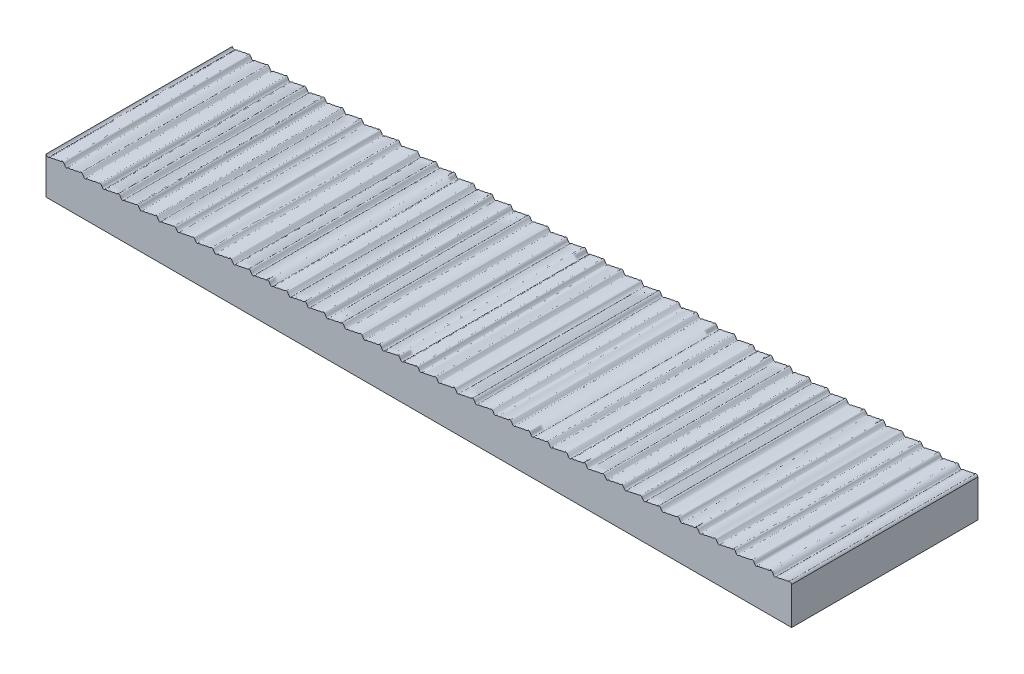
SolidWorks part; units mm, degrees
ref_plane "Ebene vorne" through (0, 0, 0) normal (0, 0, 1) x (1, 0, 0)
ref_plane "Ebene oben" through (0, 0, 0) normal (0, 1, 0) x (1, 0, 0)
ref_plane "Ebene rechts" through (0, 0, 0) normal (1, 0, 0) x (0, 0, -1)
sketch "Skizze1" plane through (0, 0, 0) normal (0, 0, 1) x (1, 0, 0)
  line L0 (0, 10) -> (200, 10) construction
  line L1 (0, 9.5015) -> (200, 9.5015) construction
  line L2 (0, 10) -> (0, 0)
  line L3 (0, 0) -> (200, 0)
  line L4 (200, 10) -> (200, 0)
  line L5 (5.0024, 10) -> (5.0024, 0) construction
  spline S0 degree 4 poles (-19.9997, 10.0004) (-19.9561, 9.9393) (-19.8702, 9.8101) (-19.7695, 9.5768) (-19.4484, 9.4333) (-19.1776, 9.6437) (-18.9243, 9.8025) (-18.5526, 9.7578) (-18.1555, 9.7858) (-17.7539, 10.092) (-17.2072, 9.9072) (-16.8128, 10.2432) (-16.411, 10.2274) (-16.0478, 10.2076) (-15.8056, 10.3731) (-15.5379, 10.5654) (-15.239, 10.4178) (-15.109, 10.1453) (-14.9267, 9.9253) (-14.8002, 9.6012) (-14.3654, 9.35) (-14.0196, 9.9267) (-13.4696, 9.656) (-13.0108, 9.9529) (-12.5208, 10.0184) (-12.0494, 9.999) (-11.6793, 10.2867) (-11.286, 10.195) (-10.9422, 10.2339) (-10.6975, 10.5008) (-10.3481, 10.5321) (-10.1558, 10.2486) (-9.9931, 9.9984) (-9.8662, 9.7615) (-9.5445, 9.3399) (-9.1467, 9.7133) (-8.7378, 9.8283) (-8.2063, 9.709) (-7.8111, 10.0928) (-7.3039, 9.9246) (-6.9101, 10.1513) (-6.5245, 10.2729) (-6.0945, 10.1604) (-5.8142, 10.3786) (-5.4938, 10.5774) (-5.2167, 10.3703) (-5.0931, 10.1352) (-4.9179, 9.9003) (-4.795, 9.6045) (-4.4149, 9.3823) (-4.0837, 9.7842) (-3.6892, 9.7915) (-3.2241, 9.7344) (-2.8526, 10.0555) (-2.3492, 9.9445) (-1.9311, 10.1231) (-1.4459, 10.3184) (-0.9596, 10.0819) (-0.5308, 10.785) (-0.092, 10.1614) (0.0169, 9.9695) (0.2349, 9.6114) (0.4997, 9.4251) (0.8435, 9.6511) (1.1124, 9.8359) (1.5017, 9.7362) (1.8057, 9.8153) (2.0544, 9.9415) (2.3055, 10.0076) (2.5787, 9.9953) (2.8778, 10.016) (3.1891, 10.2002) (3.549, 10.2647) (4.0061, 10.1497) (4.2833, 10.5328) (4.702, 10.5168) (4.8822, 10.1617) (5.0607, 9.9339) (5.1997, 9.6313) (5.5064, 9.4113) (5.8209, 9.6409) (6.0917, 9.8146) (6.4582, 9.7552) (6.7962, 9.7866) (7.1194, 9.9965) (7.4888, 10.0034) (7.8588, 9.9936) (8.1922, 10.2082) (8.5409, 10.2506) (8.9496, 10.1737) (9.2146, 10.416) (9.58, 10.5878) (9.8433, 10.2719) (9.9989, 10.0022) (10.1563, 9.728) (10.4232, 9.4068) (10.7886, 9.59) (11.0551, 9.8225) (11.4498, 9.752) (11.7948, 9.7868) (12.1246, 9.998) (12.4939, 10.0025) (12.8637, 9.9953) (13.1968, 10.2111) (13.5462, 10.2492) (13.9548, 10.1743) (14.2183, 10.4214) (14.5863, 10.5859) (14.8452, 10.2663) (15.0021, 9.9987) (15.1582, 9.7222) (15.4295, 9.4052) (15.7922, 9.5954) (16.0602, 9.823) (16.455, 9.7508) (16.7993, 9.7893) (17.1292, 9.9999) (17.4986, 10.0011) (17.8685, 9.9974) (18.1999, 10.2127) (18.5525, 10.2491) (18.9557, 10.1728) (19.2232, 10.4273) (19.5922, 10.5837) (19.8472, 10.2608) (20.0052, 9.9953) (20.1602, 9.7165) (20.4358, 9.4038) (20.7959, 9.6007) (21.0654, 9.8235) (21.4603, 9.7495) (21.8039, 9.7919) (22.1339, 10.0019) (22.5039, 9.9999) (22.8733, 9.9993) (23.2045, 10.2154) (23.5579, 10.2478) (23.9608, 10.1736) (24.227, 10.4327) (24.5984, 10.5816) (24.8491, 10.2554) (25.0084, 9.9918) (25.1623, 9.7108) (25.4422, 9.4025) (25.7994, 9.606) (26.0707, 9.8238) (26.4655, 9.7483) (26.8086, 9.7945) (27.1386, 10.0038) (27.5093, 9.9987) (27.878, 10.0013) (28.2092, 10.2179) (28.5633, 10.2463) (28.9658, 10.1744) (29.2308, 10.438) (29.6045, 10.5793) (29.851, 10.25) (30.0116, 9.9884) (30.1643, 9.705) (30.4486, 9.4014) (30.8029, 9.6113) (31.076, 9.8242) (31.4707, 9.7472) (31.8132, 9.7971) (32.1433, 10.0056) (32.5147, 9.9975) (32.8827, 10.0034) (33.2139, 10.2205) (33.5687, 10.2449) (33.9708, 10.1753) (34.2347, 10.4433) (34.6105, 10.5768) (34.8528, 10.2446) (35.0148, 9.985) (35.1663, 9.6993) (35.4549, 9.4004) (35.8063, 9.6165) (36.0813, 9.8244) (36.4759, 9.746) (36.8179, 9.7998) (37.148, 10.0075) (37.5201, 9.9962) (37.8873, 10.0057) (38.2187, 10.2227) (38.5737, 10.2439) (38.9763, 10.1755) (39.2407, 10.4527) (39.6307, 10.576) (39.8665, 10.2116) (40.0383, 9.9585) (40.1921, 9.6374) (40.5168, 9.4039) (40.8355, 9.6598) (41.1108, 9.8146) (41.4929, 9.7484) (41.8256, 9.8036) (42.153, 10.0098) (42.5253, 9.9946) (42.8921, 10.008) (43.2233, 10.225) (43.5792, 10.2424) (43.981, 10.1766) (44.2447, 10.458) (44.6365, 10.573) (44.8682, 10.2065) (45.0412, 9.9553) (45.1946, 9.6316) (45.5229, 9.4047) (45.8387, 9.6643) (46.1164, 9.8146) (46.4978, 9.7474) (46.8303, 9.8065) (47.1577, 10.0114) (47.5307, 9.9935) (47.8968, 10.0101) (48.2278, 10.2277) (48.5849, 10.2403) (48.9852, 10.1788) (49.2459, 10.4577) (49.6244, 10.5683) (49.8544, 10.2369) (50.0188, 9.9811) (50.166, 9.6982) (50.4577, 9.4005) (50.8095, 9.6157) (51.0859, 9.829) (51.4904, 9.7412) (51.8293, 9.8082) (52.1631, 10.012) (52.5356, 9.9928) (52.9017, 10.0121) (53.2323, 10.2301) (53.5904, 10.2387) (53.9899, 10.1802) (54.2499, 10.4628) (54.6301, 10.5654) (54.8562, 10.2318) (55.0219, 9.9776) (55.1681, 9.6925) (55.464, 9.3997) (55.8131, 9.6212) (56.0912, 9.8289) (56.4956, 9.7403) (56.8339, 9.811) (57.1679, 10.0136) (57.541, 9.9916) (57.9063, 10.0144) (58.2369, 10.2323) (58.5958, 10.2371) (58.9945, 10.1815) (59.254, 10.4678) (59.6359, 10.5624) (59.858, 10.2269) (60.025, 9.9741) (60.1702, 9.6868) (60.4702, 9.3989) (60.8166, 9.6266) (61.0966, 9.8287) (61.5007, 9.7394) (61.8385, 9.8139) (62.1727, 10.0151) (62.5463, 9.9904) (62.911, 10.0168) (63.2416, 10.2345) (63.6012, 10.2355) (63.9991, 10.183) (64.2582, 10.4728) (64.6415, 10.5592) (64.8598, 10.2219) (65.0281, 9.9707) (65.1724, 9.6811) (65.4765, 9.3984) (65.8201, 9.632) (66.102, 9.8284) (66.5058, 9.7385) (66.8431, 9.8168) (67.1775, 10.0165) (67.5516, 9.9893) (67.9156, 10.0192) (68.2462, 10.2366) (68.6067, 10.2339) (69.0036, 10.1846) (69.2623, 10.4778) (69.647, 10.556) (69.8615, 10.2171) (70.0311, 9.9672) (70.1746, 9.6754) (70.4827, 9.398) (70.8236, 9.6374) (71.1074, 9.8281) (71.5109, 9.7377) (71.8477, 9.8197) (72.1824, 10.0179) (72.5569, 9.9881) (72.9202, 10.0217) (73.2508, 10.2387) (73.6122, 10.2323) (74.008, 10.1863) (74.2666, 10.4827) (74.6525, 10.5526) (74.8633, 10.2123) (75.0342, 9.9637) (75.1768, 9.6697) (75.4889, 9.3977) (75.827, 9.6427) (76.1129, 9.8278) (76.5159, 9.7369) (76.8526, 9.8228) (77.1873, 10.0192) (77.563, 9.9871) (77.9249, 10.0241) (78.2569, 10.2418) (78.618, 10.2295) (79.0102, 10.1872) (79.2717, 10.4879) (79.6574, 10.5489) (79.8653, 10.2077) (80.037, 9.9602) (80.1792, 9.664) (80.495, 9.3976) (80.8303, 9.648) (81.1184, 9.8273) (81.521, 9.7361) (81.8572, 9.8259) (82.1922, 10.0204) (82.5683, 9.986) (82.9296, 10.0267) (83.2615, 10.2437) (83.6237, 10.2278) (84.0145, 10.189) (84.276, 10.4926) (84.6627, 10.5453) (84.8671, 10.2031) (85.0399, 9.9567) (85.1815, 9.6584) (85.5012, 9.3976) (85.8337, 9.6533) (86.124, 9.8268) (86.526, 9.7354) (86.8618, 9.8289) (87.1971, 10.0216) (87.5736, 9.9849) (87.9342, 10.0293) (88.2661, 10.2456) (88.6293, 10.2262) (89.0188, 10.191) (89.2804, 10.4973) (89.668, 10.5416) (89.8688, 10.1985) (90.0429, 9.9532) (90.1839, 9.6527) (90.5073, 9.3978) (90.837, 9.6585) (91.1296, 9.8263) (91.531, 9.7348) (91.8666, 9.832) (92.202, 10.0228) (92.5793, 9.9837) (92.9389, 10.0323) (93.2714, 10.2474) (93.6347, 10.2247) (94.0244, 10.193) (94.2842, 10.501) (94.6728, 10.5389) (94.871, 10.1929) (95.0455, 9.9509) (95.1865, 9.6454) (95.5132, 9.4008) (95.8406, 9.6584) (96.1347, 9.8335) (96.5739, 9.7092) (96.9573, 9.9087) (97.4027, 10.049) (97.928, 9.9505) (98.349, 10.3706) (98.9393, 10.0547) (99.2714, 10.5624) (99.7397, 10.4986) (99.9143, 10.1026) (100.0854, 9.8974) (100.2534, 9.5137) (100.7088, 9.4268) (101.034, 9.9297) (101.6028, 9.6422) (102.0297, 10.0051) (102.5416, 9.9848) (102.9924, 10.0402) (103.3656, 10.2905) (103.764, 10.1834) (104.0914, 10.2634) (104.3345, 10.5287) (104.6796, 10.5058) (104.8496, 10.2313) (105.0099, 9.9981) (105.1412, 9.7482) (105.472, 9.3179) (105.8907, 9.7622) (106.3041, 9.8037) (106.8229, 9.7381) (107.1977, 10.081) (107.6865, 9.9328) (108.0835, 10.1397) (108.4713, 10.285) (108.9328, 10.1425) (109.2161, 10.4309) (109.5896, 10.5754) (109.8314, 10.2832) (109.9871, 10.0239) (110.123, 9.7872) (110.4598, 9.3001) (110.8914, 9.782) (111.343, 9.7746) (111.8796, 9.7812) (112.3018, 10.0998) (112.8194, 9.9178) (113.1916, 10.2408) (113.5924, 10.2319) (113.9843, 10.1841) (114.2454, 10.4523) (114.5965, 10.5606) (114.8238, 10.2968) (114.9712, 10.0385) (115.1177, 9.8205) (115.359, 9.4027) (115.7941, 9.5621) (116.1197, 9.89) (116.6444, 9.6688) (117.0207, 9.9811) (117.4676, 10.01) (117.9172, 9.988) (118.2724, 10.2873) (118.7495, 10.1792) (119.114, 10.2688) (119.5483, 10.6931) (119.9526, 10.1364) (120.0518, 9.8537) (120.4599, 9.3153) (120.8803, 9.7298) (121.2533, 9.8219) (121.7411, 9.7114) (122.1, 10.0262) (122.5565, 9.9798) (122.9935, 10.0364) (123.3665, 10.3239) (123.8816, 10.116) (124.2003, 10.4322) (124.634, 10.5987) (124.8782, 10.1926) (125.0212, 9.9686) (125.172, 9.717) (125.3715, 9.4617) (125.7009, 9.513) (125.9284, 9.7432) (126.2409, 9.8107) (126.6116, 9.7183) (126.9875, 9.9308) (127.4157, 10.0367) (127.9457, 9.9648) (128.3574, 10.365) (128.9456, 10.0659) (129.267, 10.5392) (129.7242, 10.5206) (129.9012, 10.1089) (130.0774, 9.9306) (130.2348, 9.5283) (130.6931, 9.4089) (131.0365, 9.942) (131.6117, 9.6335) (132.0442, 10.0209) (132.5598, 9.9733) (133.003, 10.0554) (133.3771, 10.2848) (133.7622, 10.189) (134.083, 10.2555) (134.3267, 10.5163) (134.6726, 10.5194) (134.8601, 10.2207) (135.0123, 9.9828) (135.1573, 9.7418) (135.3468, 9.4839) (135.6427, 9.4904) (135.8571, 9.6735) (136.1473, 9.8345) (136.5621, 9.6945) (136.9586, 9.9257) (137.444, 10.0327) (137.9162, 9.9819) (138.2811, 10.2648) (138.6664, 10.2234) (139.0076, 10.1887) (139.3026, 10.5462) (139.7732, 10.4914) (139.9895, 10.0113) (140.1962, 9.5628) (140.7054, 9.3993) (141.0398, 9.911) (141.5237, 9.6824) (141.9223, 9.8851) (142.3213, 10.0448) (142.7845, 9.9492) (143.159, 10.2017) (143.5981, 10.2655) (144.0405, 10.1434) (144.3998, 10.6712) (144.8928, 10.299) (145.0167, 9.9256) (145.3526, 9.3604) (145.8391, 9.6137) (146.1687, 9.8678) (146.6347, 9.6908) (146.993, 9.9458) (147.4151, 10.0323) (147.8915, 9.9525) (148.2699, 10.3164) (148.7971, 10.1426) (149.1657, 10.3407) (149.5707, 10.6404) (149.8696, 10.2272) (149.9973, 9.9968) (150.1577, 9.7478) (150.35, 9.4669) (150.7036, 9.5013) (150.9519, 9.7753) (151.3089, 9.8005) (151.706, 9.7174) (152.0796, 10.0229) (152.5538, 9.9646) (153.0411, 10.0754) (153.4364, 10.3044) (153.8532, 10.1663) (154.1431, 10.3262) (154.3593, 10.5116) (154.6573, 10.5142) (154.8446, 10.2539) (154.994, 10.0087) (155.1409, 9.7726) (155.3551, 9.4505) (155.7341, 9.5141) (156.0036, 9.8318) (156.4267, 9.7526) (156.8283, 9.7814) (157.2055, 10.0713) (157.6991, 9.92) (158.1096, 10.1852) (158.6007, 10.2628) (159.0724, 10.1494) (159.4455, 10.6796) (159.8322, 10.3242) (159.9514, 10.046) (160.13, 9.8171) (160.2682, 9.5442) (160.5961, 9.4413) (160.8513, 9.6769) (161.1349, 9.8172) (161.5235, 9.7307) (161.9075, 9.8524) (162.3262, 10.0731) (162.8577, 9.924) (163.2388, 10.2788) (163.6348, 10.2051) (163.9688, 10.2259) (164.1922, 10.3643) (164.4456, 10.5582) (164.7474, 10.4378) (164.894, 10.1511) (165.0716, 9.9148) (165.2171, 9.5733) (165.6554, 9.3779) (165.9849, 9.909) (166.5256, 9.6673) (166.9743, 9.9361) (167.4597, 10.0291) (167.9346, 9.9853) (168.3028, 10.2857) (168.7018, 10.1955) (169.0519, 10.2315) (169.2937, 10.4965) (169.6383, 10.5352) (169.8377, 10.2638) (169.9781, 10.0338) (170.13, 9.7981) (170.3405, 9.436) (170.7625, 9.5233) (171.0643, 9.8732) (171.545, 9.6966) (171.9329, 9.8883) (172.3381, 10.0454) (172.7899, 9.9533) (173.1614, 10.1966) (173.584, 10.2732) (174.0298, 10.1293) (174.3917, 10.6783) (174.8939, 10.296) (175.0212, 9.9207) (175.3751, 9.3417) (175.8507, 9.6469) (176.197, 9.853) (176.6499, 9.6984) (177.0053, 9.9495) (177.4146, 10.0315) (177.8728, 9.9532) (178.2342, 10.2897) (178.7466, 10.1669) (179.1302, 10.291) (179.5667, 10.6732) (179.8754, 10.2102) (180.0202, 9.9662) (180.1751, 9.7049) (180.4078, 9.4355) (180.7474, 9.5508) (180.9886, 9.788) (181.3462, 9.7905) (181.7288, 9.7288) (182.0942, 10.0299) (182.5671, 9.959) (183.0446, 10.0844) (183.4873, 10.3232) (184.0143, 10.1021) (184.3256, 10.5893) (184.7469, 10.4643) (184.8966, 10.1358) (185.0699, 9.9164) (185.2021, 9.6112) (185.614, 9.3537) (185.9505, 9.8827) (186.4703, 9.6945) (186.9383, 9.885) (187.4051, 10.0566) (187.8932, 9.956) (188.2611, 10.2725) (188.6557, 10.2092) (189.0217, 10.2098) (189.2654, 10.4771) (189.6333, 10.5513) (189.8421, 10.2526) (190.0111, 9.9988) (190.1397, 9.7369) (190.4628, 9.3573) (190.8593, 9.6905) (191.2201, 9.8426) (191.7298, 9.6957) (192.1002, 10.0322) (192.5644, 9.9789) (192.996, 10.0366) (193.3581, 10.3232) (193.8488, 10.1154) (194.1828, 10.4139) (194.6562, 10.6198) (194.9732, 10.0639) (195.1087, 9.7436) (195.557, 9.3091) (195.9478, 9.8405) (196.359, 9.7523) (196.8209, 9.772) (197.1867, 10.0608) (197.6927, 9.9354) (198.0939, 10.1576) (198.5842, 10.2925) (199.0526, 10.1136) (199.4823, 10.7678) (199.9593, 10.0974) (200.0429, 9.8979) (200.5304, 9.223) (200.9599, 9.912) (201.4458, 9.6856) (201.9312, 9.8744) (202.3492, 10.057) (202.8527, 9.9437) (203.2241, 10.2661) (203.6893, 10.2082) (204.0837, 10.216) (204.4149, 10.6176) (204.795, 10.3956) (204.9179, 10.0997) (205.0931, 9.8648) (205.2167, 9.6297) (205.4938, 9.4226) (205.8142, 9.6214) (206.0945, 9.8396) (206.5245, 9.7271) (206.9101, 9.8487) (207.3039, 10.0754) (207.8111, 9.9072) (208.2063, 10.291) (208.7378, 10.1717) (209.1467, 10.2867) (209.5445, 10.6601) (209.8662, 10.2385) (209.9931, 10.0016) (210.1558, 9.7514) (210.3481, 9.4679) (210.6975, 9.4992) (210.9422, 9.7661) (211.286, 9.805) (211.6793, 9.7133) (212.0494, 10.001) (212.5208, 9.9816) (213.0108, 10.0471) (213.4696, 10.344) (214.0196, 10.0733) (214.3654, 10.65) (214.8002, 10.3988) (214.9267, 10.0747) (215.109, 9.8547) (215.239, 9.5822) (215.5379, 9.4346) (215.8056, 9.6269) (216.0478, 9.7924) (216.411, 9.7726) (216.8128, 9.7568) (217.2072, 10.0928) (217.7539, 9.908) (218.1555, 10.2142) (218.5526, 10.2422) (218.9243, 10.1975) (219.1776, 10.3563) (219.4484, 10.5667) (219.7695, 10.4232) (219.8702, 10.1899) (219.9561, 10.0607) (219.9997, 9.9996) knots 0 0 0 0 0 0.001164 0.002328 0.003437 0.004546 0.005655 0.006765 0.008627 0.01049 0.012352 0.014214 0.015301 0.016387 0.017473 0.018559 0.019624 0.020688 0.021752 0.022816 0.024699 0.026583 0.028429 0.030276 0.032122 0.033968 0.035217 0.036465 0.037713 0.038961 0.04003 0.041099 0.042169 0.043238 0.044921 0.046605 0.048383 0.050161 0.051939 0.053717 0.055146 0.056575 0.058004 0.059433 0.060422 0.061411 0.062401 0.06339 0.064742 0.066094 0.067687 0.06928 0.070873 0.072466 0.07425 0.076033 0.077817 0.079601 0.081473 0.083345 0.084435 0.085525 0.086615 0.087705 0.089654 0.090629 0.091603 0.092578 0.093552 0.094527 0.095502 0.09703 0.098559 0.100088 0.101617 0.102786 0.103956 0.105126 0.106295 0.107518 0.10874 0.109963 0.111186 0.112534 0.113882 0.11523 0.116578 0.117926 0.119274 0.120622 0.12197 0.123183 0.124396 0.125609 0.126822 0.128125 0.129427 0.13073 0.132032 0.13338 0.134728 0.136076 0.137425 0.138773 0.140121 0.141469 0.142817 0.14403 0.145243 0.146456 0.147669 0.148972 0.150274 0.151576 0.152879 0.154226 0.155574 0.156921 0.158269 0.159617 0.160964 0.162312 0.163659 0.164873 0.166086 0.167299 0.168512 0.169814 0.171116 0.172418 0.173721 0.175068 0.176416 0.177764 0.179111 0.180459 0.181807 0.183154 0.184502 0.185715 0.186928 0.188142 0.189355 0.190657 0.191959 0.193261 0.194563 0.19591 0.197258 0.198606 0.199954 0.201301 0.202649 0.203997 0.205344 0.206558 0.207771 0.208984 0.210197 0.211499 0.212801 0.214103 0.215405 0.216752 0.2181 0.219448 0.220796 0.222143 0.223491 0.224839 0.226187 0.2274 0.228613 0.229827 0.23104 0.232342 0.233643 0.234945 0.236247 0.237594 0.238942 0.24029 0.241638 0.242986 0.244333 0.245681 0.247029 0.2483 0.24957 0.250841 0.252112 0.253357 0.254602 0.255847 0.257092 0.25844 0.259788 0.261136 0.262483 0.263831 0.265179 0.266527 0.267875 0.269145 0.270416 0.271686 0.272957 0.274202 0.275447 0.276692 0.277938 0.279286 0.280633 0.281981 0.283329 0.284677 0.286025 0.287373 0.28872 0.289917 0.291115 0.292312 0.293509 0.294828 0.296146 0.297465 0.298784 0.300132 0.301479 0.302827 0.304175 0.305523 0.306871 0.308218 0.309566 0.310763 0.311961 0.313158 0.314355 0.315674 0.316992 0.318311 0.31963 0.320978 0.322326 0.323673 0.325021 0.326369 0.327717 0.329065 0.330412 0.33161 0.332807 0.334004 0.335201 0.33652 0.337839 0.339158 0.340476 0.341824 0.343172 0.34452 0.345867 0.347215 0.348563 0.349911 0.351259 0.352456 0.353653 0.35485 0.356048 0.357366 0.358685 0.360004 0.361323 0.362671 0.364019 0.365366 0.366714 0.368062 0.369409 0.370757 0.372105 0.373302 0.3745 0.375697 0.376894 0.378213 0.379532 0.380851 0.38217 0.383518 0.384865 0.386213 0.387561 0.388908 0.390256 0.391604 0.392951 0.394149 0.395346 0.396543 0.397741 0.39906 0.400379 0.401698 0.403017 0.404365 0.405713 0.407062 0.40841 0.409758 0.411106 0.412455 0.413803 0.415 0.416198 0.417395 0.418592 0.419911 0.421231 0.42255 0.423869 0.425217 0.426566 0.427914 0.429262 0.43061 0.431958 0.433307 0.434655 0.435852 0.437049 0.438247 0.439444 0.440763 0.442083 0.443402 0.444722 0.44607 0.447418 0.448766 0.450114 0.451462 0.452811 0.454159 0.455507 0.456704 0.457901 0.459098 0.460296 0.461615 0.462935 0.464255 0.465574 0.466923 0.468271 0.469619 0.470968 0.472316 0.473665 0.475013 0.476361 0.477558 0.478756 0.479953 0.48115 0.48247 0.48379 0.48511 0.486429 0.488266 0.490103 0.49194 0.493777 0.495699 0.497622 0.498772 0.499922 0.501072 0.502222 0.504056 0.505889 0.507726 0.509563 0.511401 0.513238 0.514474 0.51571 0.516946 0.518182 0.519208 0.520233 0.521258 0.522284 0.524122 0.525961 0.527643 0.529325 0.531007 0.532689 0.534198 0.535706 0.537214 0.538722 0.539805 0.540888 0.541971 0.543054 0.544925 0.546797 0.548633 0.550468 0.552304 0.55414 0.555496 0.556852 0.558208 0.559564 0.560615 0.561665 0.562716 0.563766 0.565366 0.566965 0.568622 0.570279 0.571936 0.573593 0.575137 0.576681 0.578225 0.579769 0.581548 0.583327 0.585016 0.586705 0.588292 0.589879 0.591467 0.593054 0.594679 0.596303 0.597928 0.599553 0.601145 0.602737 0.603778 0.60482 0.605861 0.606902 0.608053 0.609204 0.610355 0.611507 0.613344 0.615182 0.61702 0.618858 0.620715 0.622573 0.623712 0.624851 0.62599 0.627128 0.629046 0.630963 0.632801 0.634639 0.636476 0.638314 0.639513 0.640713 0.641912 0.643112 0.644212 0.645313 0.646414 0.647515 0.64849 0.649466 0.650442 0.651417 0.653255 0.655092 0.65693 0.658767 0.659993 0.661219 0.662445 0.66367 0.665597 0.667523 0.669197 0.670872 0.672459 0.674046 0.675633 0.67722 0.678808 0.680396 0.681984 0.683571 0.685256 0.686941 0.688857 0.690772 0.69225 0.693727 0.695205 0.696682 0.698388 0.700094 0.701799 0.703505 0.705137 0.70677 0.707826 0.708883 0.709939 0.710996 0.712279 0.713563 0.714847 0.716131 0.717969 0.719806 0.721644 0.723482 0.724462 0.725442 0.726422 0.727403 0.728514 0.729624 0.730735 0.731846 0.733279 0.734713 0.736146 0.73758 0.739316 0.741053 0.74279 0.744527 0.74636 0.748193 0.749232 0.750271 0.75131 0.752349 0.75352 0.754691 0.755861 0.757032 0.75887 0.760708 0.762546 0.764384 0.76538 0.766377 0.767374 0.76837 0.769512 0.770654 0.771796 0.772938 0.774716 0.776495 0.778333 0.780171 0.782009 0.783846 0.785114 0.786382 0.78765 0.788917 0.789938 0.790959 0.79198 0.793001 0.794475 0.79595 0.797538 0.799126 0.800714 0.802302 0.803849 0.805396 0.806943 0.808489 0.810254 0.812019 0.813946 0.815872 0.817344 0.818816 0.820288 0.821759 0.82338 0.825001 0.826622 0.828242 0.830054 0.831865 0.832959 0.834054 0.835148 0.836242 0.837483 0.838724 0.839966 0.841207 0.84303 0.844853 0.846676 0.848499 0.850195 0.85189 0.852953 0.854016 0.855079 0.856142 0.857907 0.859672 0.861509 0.863346 0.865183 0.86702 0.868304 0.869588 0.870872 0.872155 0.873282 0.874408 0.875534 0.87666 0.878259 0.879858 0.881512 0.883166 0.88482 0.886474 0.888022 0.88957 0.891118 0.892666 0.894441 0.896217 0.897907 0.899598 0.901182 0.902765 0.904349 0.905933 0.90769 0.909448 0.911205 0.912962 0.914809 0.916655 0.918527 0.920399 0.922183 0.923967 0.92575 0.927534 0.929127 0.93072 0.932313 0.933906 0.935258 0.93661 0.937599 0.938589 0.939578 0.940567 0.941996 0.943425 0.944854 0.946283 0.948061 0.949839 0.951617 0.953395 0.955079 0.956762 0.957831 0.958901 0.95997 0.961039 0.962287 0.963535 0.964783 0.966032 0.967878 0.969724 0.971571 0.973417 0.975301 0.977184 0.978248 0.979312 0.980376 0.981441 0.982527 0.983613 0.984699 0.985786 0.987648 0.98951 0.991373 0.993235 0.994345 0.995454 0.996563 0.997672 0.998836 1 1 1 1 1 construction
  spline S1 degree 4 poles (0, 10) (0.032, 9.9473) (0.0963, 9.8391) (0.2349, 9.6114) (0.4997, 9.4251) (0.8435, 9.6511) (1.1124, 9.8359) (1.5017, 9.7362) (1.8057, 9.8153) (2.0544, 9.9415) (2.3055, 10.0076) (2.5787, 9.9953) (2.8778, 10.016) (3.1891, 10.2002) (3.549, 10.2647) (4.0061, 10.1497) (4.2833, 10.5328) (4.702, 10.5168) (4.8822, 10.1617) (5.0607, 9.9339) (5.1997, 9.6313) (5.5064, 9.4113) (5.8209, 9.6409) (6.0917, 9.8146) (6.4582, 9.7552) (6.7962, 9.7866) (7.1194, 9.9965) (7.4888, 10.0034) (7.8588, 9.9936) (8.1922, 10.2082) (8.5409, 10.2506) (8.9496, 10.1737) (9.2146, 10.416) (9.58, 10.5878) (9.8433, 10.2719) (9.9989, 10.0022) (10.1563, 9.728) (10.4232, 9.4068) (10.7886, 9.59) (11.0551, 9.8225) (11.4498, 9.752) (11.7948, 9.7868) (12.1246, 9.998) (12.4939, 10.0025) (12.8637, 9.9953) (13.1968, 10.2111) (13.5462, 10.2492) (13.9548, 10.1743) (14.2183, 10.4214) (14.5863, 10.5859) (14.8452, 10.2663) (15.0021, 9.9987) (15.1582, 9.7222) (15.4295, 9.4052) (15.7922, 9.5954) (16.0602, 9.823) (16.455, 9.7508) (16.7993, 9.7893) (17.1292, 9.9999) (17.4986, 10.0011) (17.8685, 9.9974) (18.1999, 10.2127) (18.5525, 10.2491) (18.9557, 10.1728) (19.2232, 10.4273) (19.5922, 10.5837) (19.8472, 10.2608) (20.0052, 9.9953) (20.1602, 9.7165) (20.4358, 9.4038) (20.7959, 9.6007) (21.0654, 9.8235) (21.4603, 9.7495) (21.8039, 9.7919) (22.1339, 10.0019) (22.5039, 9.9999) (22.8733, 9.9993) (23.2045, 10.2154) (23.5579, 10.2478) (23.9608, 10.1736) (24.227, 10.4327) (24.5984, 10.5816) (24.8491, 10.2554) (25.0084, 9.9918) (25.1623, 9.7108) (25.4422, 9.4025) (25.7994, 9.606) (26.0707, 9.8238) (26.4655, 9.7483) (26.8086, 9.7945) (27.1386, 10.0038) (27.5093, 9.9987) (27.878, 10.0013) (28.2092, 10.2179) (28.5633, 10.2463) (28.9658, 10.1744) (29.2308, 10.438) (29.6045, 10.5793) (29.851, 10.25) (30.0116, 9.9884) (30.1643, 9.705) (30.4486, 9.4014) (30.8029, 9.6113) (31.076, 9.8242) (31.4707, 9.7472) (31.8132, 9.7971) (32.1433, 10.0056) (32.5147, 9.9975) (32.8827, 10.0034) (33.2139, 10.2205) (33.5687, 10.2449) (33.9708, 10.1753) (34.2347, 10.4433) (34.6105, 10.5768) (34.8528, 10.2446) (35.0148, 9.985) (35.1663, 9.6993) (35.4549, 9.4004) (35.8063, 9.6165) (36.0813, 9.8244) (36.4759, 9.746) (36.8179, 9.7998) (37.148, 10.0075) (37.5201, 9.9962) (37.8873, 10.0057) (38.2187, 10.2227) (38.5737, 10.2439) (38.9763, 10.1755) (39.2407, 10.4527) (39.6307, 10.576) (39.8665, 10.2116) (40.0383, 9.9585) (40.1921, 9.6374) (40.5168, 9.4039) (40.8355, 9.6598) (41.1108, 9.8146) (41.4929, 9.7484) (41.8256, 9.8036) (42.153, 10.0098) (42.5253, 9.9946) (42.8921, 10.008) (43.2233, 10.225) (43.5792, 10.2424) (43.981, 10.1766) (44.2447, 10.458) (44.6365, 10.573) (44.8682, 10.2065) (45.0412, 9.9553) (45.1946, 9.6316) (45.5229, 9.4047) (45.8387, 9.6643) (46.1164, 9.8146) (46.4978, 9.7474) (46.8303, 9.8065) (47.1577, 10.0114) (47.5307, 9.9935) (47.8968, 10.0101) (48.2278, 10.2277) (48.5849, 10.2403) (48.9852, 10.1788) (49.2459, 10.4577) (49.6244, 10.5683) (49.8544, 10.2369) (50.0188, 9.9811) (50.166, 9.6982) (50.4577, 9.4005) (50.8095, 9.6157) (51.0859, 9.829) (51.4904, 9.7412) (51.8293, 9.8082) (52.1631, 10.012) (52.5356, 9.9928) (52.9017, 10.0121) (53.2323, 10.2301) (53.5904, 10.2387) (53.9899, 10.1802) (54.2499, 10.4628) (54.6301, 10.5654) (54.8562, 10.2318) (55.0219, 9.9776) (55.1681, 9.6925) (55.464, 9.3997) (55.8131, 9.6212) (56.0912, 9.8289) (56.4956, 9.7403) (56.8339, 9.811) (57.1679, 10.0136) (57.541, 9.9916) (57.9063, 10.0144) (58.2369, 10.2323) (58.5958, 10.2371) (58.9945, 10.1815) (59.254, 10.4678) (59.6359, 10.5624) (59.858, 10.2269) (60.025, 9.9741) (60.1702, 9.6868) (60.4702, 9.3989) (60.8166, 9.6266) (61.0966, 9.8287) (61.5007, 9.7394) (61.8385, 9.8139) (62.1727, 10.0151) (62.5463, 9.9904) (62.911, 10.0168) (63.2416, 10.2345) (63.6012, 10.2355) (63.9991, 10.183) (64.2582, 10.4728) (64.6415, 10.5592) (64.8598, 10.2219) (65.0281, 9.9707) (65.1724, 9.6811) (65.4765, 9.3984) (65.8201, 9.632) (66.102, 9.8284) (66.5058, 9.7385) (66.8431, 9.8168) (67.1775, 10.0165) (67.5516, 9.9893) (67.9156, 10.0192) (68.2462, 10.2366) (68.6067, 10.2339) (69.0036, 10.1846) (69.2623, 10.4778) (69.647, 10.556) (69.8615, 10.2171) (70.0311, 9.9672) (70.1746, 9.6754) (70.4827, 9.398) (70.8236, 9.6374) (71.1074, 9.8281) (71.5109, 9.7377) (71.8477, 9.8197) (72.1824, 10.0179) (72.5569, 9.9881) (72.9202, 10.0217) (73.2508, 10.2387) (73.6122, 10.2323) (74.008, 10.1863) (74.2666, 10.4827) (74.6525, 10.5526) (74.8633, 10.2123) (75.0342, 9.9637) (75.1768, 9.6697) (75.4889, 9.3977) (75.827, 9.6427) (76.1129, 9.8278) (76.5159, 9.7369) (76.8526, 9.8228) (77.1873, 10.0192) (77.563, 9.9871) (77.9249, 10.0241) (78.2569, 10.2418) (78.618, 10.2295) (79.0102, 10.1872) (79.2717, 10.4879) (79.6574, 10.5489) (79.8653, 10.2077) (80.037, 9.9602) (80.1792, 9.664) (80.495, 9.3976) (80.8303, 9.648) (81.1184, 9.8273) (81.521, 9.7361) (81.8572, 9.8259) (82.1922, 10.0204) (82.5683, 9.986) (82.9296, 10.0267) (83.2615, 10.2437) (83.6237, 10.2278) (84.0145, 10.189) (84.276, 10.4926) (84.6627, 10.5453) (84.8671, 10.2031) (85.0399, 9.9567) (85.1815, 9.6584) (85.5012, 9.3976) (85.8337, 9.6533) (86.124, 9.8268) (86.526, 9.7354) (86.8618, 9.8289) (87.1971, 10.0216) (87.5736, 9.9849) (87.9342, 10.0293) (88.2661, 10.2456) (88.6293, 10.2262) (89.0188, 10.191) (89.2804, 10.4973) (89.668, 10.5416) (89.8688, 10.1985) (90.0429, 9.9532) (90.1839, 9.6527) (90.5073, 9.3978) (90.837, 9.6585) (91.1296, 9.8263) (91.531, 9.7348) (91.8666, 9.832) (92.202, 10.0228) (92.5793, 9.9837) (92.9389, 10.0323) (93.2714, 10.2474) (93.6347, 10.2247) (94.0244, 10.193) (94.2842, 10.501) (94.6728, 10.5389) (94.871, 10.1929) (95.0455, 9.9509) (95.1865, 9.6454) (95.5132, 9.4008) (95.8406, 9.6584) (96.1347, 9.8335) (96.5739, 9.7092) (96.9573, 9.9087) (97.4027, 10.049) (97.928, 9.9505) (98.349, 10.3706) (98.9393, 10.0547) (99.2714, 10.5624) (99.7397, 10.4986) (99.9143, 10.1026) (100.0854, 9.8974) (100.2534, 9.5137) (100.7088, 9.4268) (101.034, 9.9297) (101.6028, 9.6422) (102.0297, 10.0051) (102.5416, 9.9848) (102.9924, 10.0402) (103.3656, 10.2905) (103.764, 10.1834) (104.0914, 10.2634) (104.3345, 10.5287) (104.6796, 10.5058) (104.8496, 10.2313) (105.0099, 9.9981) (105.1412, 9.7482) (105.472, 9.3179) (105.8907, 9.7622) (106.3041, 9.8037) (106.8229, 9.7381) (107.1977, 10.081) (107.6865, 9.9328) (108.0835, 10.1397) (108.4713, 10.285) (108.9328, 10.1425) (109.2161, 10.4309) (109.5896, 10.5754) (109.8314, 10.2832) (109.9871, 10.0239) (110.123, 9.7872) (110.4598, 9.3001) (110.8914, 9.782) (111.343, 9.7746) (111.8796, 9.7812) (112.3018, 10.0998) (112.8194, 9.9178) (113.1916, 10.2408) (113.5924, 10.2319) (113.9843, 10.1841) (114.2454, 10.4523) (114.5965, 10.5606) (114.8238, 10.2968) (114.9712, 10.0385) (115.1177, 9.8205) (115.359, 9.4027) (115.7941, 9.5621) (116.1197, 9.89) (116.6444, 9.6688) (117.0207, 9.9811) (117.4676, 10.01) (117.9172, 9.988) (118.2724, 10.2873) (118.7495, 10.1792) (119.114, 10.2688) (119.5483, 10.6931) (119.9526, 10.1364) (120.0518, 9.8537) (120.4599, 9.3153) (120.8803, 9.7298) (121.2533, 9.8219) (121.7411, 9.7114) (122.1, 10.0262) (122.5565, 9.9798) (122.9935, 10.0364) (123.3665, 10.3239) (123.8816, 10.116) (124.2003, 10.4322) (124.634, 10.5987) (124.8782, 10.1926) (125.0212, 9.9686) (125.172, 9.717) (125.3715, 9.4617) (125.7009, 9.513) (125.9284, 9.7432) (126.2409, 9.8107) (126.6116, 9.7183) (126.9875, 9.9308) (127.4157, 10.0367) (127.9457, 9.9648) (128.3574, 10.365) (128.9456, 10.0659) (129.267, 10.5392) (129.7242, 10.5206) (129.9012, 10.1089) (130.0774, 9.9306) (130.2348, 9.5283) (130.6931, 9.4089) (131.0365, 9.942) (131.6117, 9.6335) (132.0442, 10.0209) (132.5598, 9.9733) (133.003, 10.0554) (133.3771, 10.2848) (133.7622, 10.189) (134.083, 10.2555) (134.3267, 10.5163) (134.6726, 10.5194) (134.8601, 10.2207) (135.0123, 9.9828) (135.1573, 9.7418) (135.3468, 9.4839) (135.6427, 9.4904) (135.8571, 9.6735) (136.1473, 9.8345) (136.5621, 9.6945) (136.9586, 9.9257) (137.444, 10.0327) (137.9162, 9.9819) (138.2811, 10.2648) (138.6664, 10.2234) (139.0076, 10.1887) (139.3026, 10.5462) (139.7732, 10.4914) (139.9895, 10.0113) (140.1962, 9.5628) (140.7054, 9.3993) (141.0398, 9.911) (141.5237, 9.6824) (141.9223, 9.8851) (142.3213, 10.0448) (142.7845, 9.9492) (143.159, 10.2017) (143.5981, 10.2655) (144.0405, 10.1434) (144.3998, 10.6712) (144.8928, 10.299) (145.0167, 9.9256) (145.3526, 9.3604) (145.8391, 9.6137) (146.1687, 9.8678) (146.6347, 9.6908) (146.993, 9.9458) (147.4151, 10.0323) (147.8915, 9.9525) (148.2699, 10.3164) (148.7971, 10.1426) (149.1657, 10.3407) (149.5707, 10.6404) (149.8696, 10.2272) (149.9973, 9.9968) (150.1577, 9.7478) (150.35, 9.4669) (150.7036, 9.5013) (150.9519, 9.7753) (151.3089, 9.8005) (151.706, 9.7174) (152.0796, 10.0229) (152.5538, 9.9646) (153.0411, 10.0754) (153.4364, 10.3044) (153.8532, 10.1663) (154.1431, 10.3262) (154.3593, 10.5116) (154.6573, 10.5142) (154.8446, 10.2539) (154.994, 10.0087) (155.1409, 9.7726) (155.3551, 9.4505) (155.7341, 9.5141) (156.0036, 9.8318) (156.4267, 9.7526) (156.8283, 9.7814) (157.2055, 10.0713) (157.6991, 9.92) (158.1096, 10.1852) (158.6007, 10.2628) (159.0724, 10.1494) (159.4455, 10.6796) (159.8322, 10.3242) (159.9514, 10.046) (160.13, 9.8171) (160.2682, 9.5442) (160.5961, 9.4413) (160.8513, 9.6769) (161.1349, 9.8172) (161.5235, 9.7307) (161.9075, 9.8524) (162.3262, 10.0731) (162.8577, 9.924) (163.2388, 10.2788) (163.6348, 10.2051) (163.9688, 10.2259) (164.1922, 10.3643) (164.4456, 10.5582) (164.7474, 10.4378) (164.894, 10.1511) (165.0716, 9.9148) (165.2171, 9.5733) (165.6554, 9.3779) (165.9849, 9.909) (166.5256, 9.6673) (166.9743, 9.9361) (167.4597, 10.0291) (167.9346, 9.9853) (168.3028, 10.2857) (168.7018, 10.1955) (169.0519, 10.2315) (169.2937, 10.4965) (169.6383, 10.5352) (169.8377, 10.2638) (169.9781, 10.0338) (170.13, 9.7981) (170.3405, 9.436) (170.7625, 9.5233) (171.0643, 9.8732) (171.545, 9.6966) (171.9329, 9.8883) (172.3381, 10.0454) (172.7899, 9.9533) (173.1614, 10.1966) (173.584, 10.2732) (174.0298, 10.1293) (174.3917, 10.6783) (174.8939, 10.296) (175.0212, 9.9207) (175.3751, 9.3417) (175.8507, 9.6469) (176.197, 9.853) (176.6499, 9.6984) (177.0053, 9.9495) (177.4146, 10.0315) (177.8728, 9.9532) (178.2342, 10.2897) (178.7466, 10.1669) (179.1302, 10.291) (179.5667, 10.6732) (179.8754, 10.2102) (180.0202, 9.9662) (180.1751, 9.7049) (180.4078, 9.4355) (180.7474, 9.5508) (180.9886, 9.788) (181.3462, 9.7905) (181.7288, 9.7288) (182.0942, 10.0299) (182.5671, 9.959) (183.0446, 10.0844) (183.4873, 10.3232) (184.0143, 10.1021) (184.3256, 10.5893) (184.7469, 10.4643) (184.8966, 10.1358) (185.0699, 9.9164) (185.2021, 9.6112) (185.614, 9.3537) (185.9505, 9.8827) (186.4703, 9.6945) (186.9383, 9.885) (187.4051, 10.0566) (187.8932, 9.956) (188.2611, 10.2725) (188.6557, 10.2092) (189.0217, 10.2098) (189.2654, 10.4771) (189.6333, 10.5513) (189.8421, 10.2526) (190.0111, 9.9988) (190.1397, 9.7369) (190.4628, 9.3573) (190.8593, 9.6905) (191.2201, 9.8426) (191.7298, 9.6957) (192.1002, 10.0322) (192.5644, 9.9789) (192.996, 10.0366) (193.3581, 10.3232) (193.8488, 10.1154) (194.1828, 10.4139) (194.6562, 10.6198) (194.9732, 10.0639) (195.1087, 9.7436) (195.557, 9.3091) (195.9478, 9.8405) (196.359, 9.7523) (196.8209, 9.772) (197.1867, 10.0608) (197.6927, 9.9354) (198.0939, 10.1576) (198.5842, 10.2925) (199.0526, 10.1136) (199.4823, 10.7678) (199.8373, 10.2688) (199.9458, 10.0893) (200, 10) knots 0.083345 0.083345 0.083345 0.083345 0.083345 0.084435 0.085525 0.086615 0.087705 0.089654 0.090629 0.091603 0.092578 0.093552 0.094527 0.095502 0.09703 0.098559 0.100088 0.101617 0.102786 0.103956 0.105126 0.106295 0.107518 0.10874 0.109963 0.111186 0.112534 0.113882 0.11523 0.116578 0.117926 0.119274 0.120622 0.12197 0.123183 0.124396 0.125609 0.126822 0.128125 0.129427 0.13073 0.132032 0.13338 0.134728 0.136076 0.137425 0.138773 0.140121 0.141469 0.142817 0.14403 0.145243 0.146456 0.147669 0.148972 0.150274 0.151576 0.152879 0.154226 0.155574 0.156921 0.158269 0.159617 0.160964 0.162312 0.163659 0.164873 0.166086 0.167299 0.168512 0.169814 0.171116 0.172418 0.173721 0.175068 0.176416 0.177764 0.179111 0.180459 0.181807 0.183154 0.184502 0.185715 0.186928 0.188142 0.189355 0.190657 0.191959 0.193261 0.194563 0.19591 0.197258 0.198606 0.199954 0.201301 0.202649 0.203997 0.205344 0.206558 0.207771 0.208984 0.210197 0.211499 0.212801 0.214103 0.215405 0.216752 0.2181 0.219448 0.220796 0.222143 0.223491 0.224839 0.226187 0.2274 0.228613 0.229827 0.23104 0.232342 0.233643 0.234945 0.236247 0.237594 0.238942 0.24029 0.241638 0.242986 0.244333 0.245681 0.247029 0.2483 0.24957 0.250841 0.252112 0.253357 0.254602 0.255847 0.257092 0.25844 0.259788 0.261136 0.262483 0.263831 0.265179 0.266527 0.267875 0.269145 0.270416 0.271686 0.272957 0.274202 0.275447 0.276692 0.277938 0.279286 0.280633 0.281981 0.283329 0.284677 0.286025 0.287373 0.28872 0.289917 0.291115 0.292312 0.293509 0.294828 0.296146 0.297465 0.298784 0.300132 0.301479 0.302827 0.304175 0.305523 0.306871 0.308218 0.309566 0.310763 0.311961 0.313158 0.314355 0.315674 0.316992 0.318311 0.31963 0.320978 0.322326 0.323673 0.325021 0.326369 0.327717 0.329065 0.330412 0.33161 0.332807 0.334004 0.335201 0.33652 0.337839 0.339158 0.340476 0.341824 0.343172 0.34452 0.345867 0.347215 0.348563 0.349911 0.351259 0.352456 0.353653 0.35485 0.356048 0.357366 0.358685 0.360004 0.361323 0.362671 0.364019 0.365366 0.366714 0.368062 0.369409 0.370757 0.372105 0.373302 0.3745 0.375697 0.376894 0.378213 0.379532 0.380851 0.38217 0.383518 0.384865 0.386213 0.387561 0.388908 0.390256 0.391604 0.392951 0.394149 0.395346 0.396543 0.397741 0.39906 0.400379 0.401698 0.403017 0.404365 0.405713 0.407062 0.40841 0.409758 0.411106 0.412455 0.413803 0.415 0.416198 0.417395 0.418592 0.419911 0.421231 0.42255 0.423869 0.425217 0.426566 0.427914 0.429262 0.43061 0.431958 0.433307 0.434655 0.435852 0.437049 0.438247 0.439444 0.440763 0.442083 0.443402 0.444722 0.44607 0.447418 0.448766 0.450114 0.451462 0.452811 0.454159 0.455507 0.456704 0.457901 0.459098 0.460296 0.461615 0.462935 0.464255 0.465574 0.466923 0.468271 0.469619 0.470968 0.472316 0.473665 0.475013 0.476361 0.477558 0.478756 0.479953 0.48115 0.48247 0.48379 0.48511 0.486429 0.488266 0.490103 0.49194 0.493777 0.495699 0.497622 0.498772 0.499922 0.501072 0.502222 0.504056 0.505889 0.507726 0.509563 0.511401 0.513238 0.514474 0.51571 0.516946 0.518182 0.519208 0.520233 0.521258 0.522284 0.524122 0.525961 0.527643 0.529325 0.531007 0.532689 0.534198 0.535706 0.537214 0.538722 0.539805 0.540888 0.541971 0.543054 0.544925 0.546797 0.548633 0.550468 0.552304 0.55414 0.555496 0.556852 0.558208 0.559564 0.560615 0.561665 0.562716 0.563766 0.565366 0.566965 0.568622 0.570279 0.571936 0.573593 0.575137 0.576681 0.578225 0.579769 0.581548 0.583327 0.585016 0.586705 0.588292 0.589879 0.591467 0.593054 0.594679 0.596303 0.597928 0.599553 0.601145 0.602737 0.603778 0.60482 0.605861 0.606902 0.608053 0.609204 0.610355 0.611507 0.613344 0.615182 0.61702 0.618858 0.620715 0.622573 0.623712 0.624851 0.62599 0.627128 0.629046 0.630963 0.632801 0.634639 0.636476 0.638314 0.639513 0.640713 0.641912 0.643112 0.644212 0.645313 0.646414 0.647515 0.64849 0.649466 0.650442 0.651417 0.653255 0.655092 0.65693 0.658767 0.659993 0.661219 0.662445 0.66367 0.665597 0.667523 0.669197 0.670872 0.672459 0.674046 0.675633 0.67722 0.678808 0.680396 0.681984 0.683571 0.685256 0.686941 0.688857 0.690772 0.69225 0.693727 0.695205 0.696682 0.698388 0.700094 0.701799 0.703505 0.705137 0.70677 0.707826 0.708883 0.709939 0.710996 0.712279 0.713563 0.714847 0.716131 0.717969 0.719806 0.721644 0.723482 0.724462 0.725442 0.726422 0.727403 0.728514 0.729624 0.730735 0.731846 0.733279 0.734713 0.736146 0.73758 0.739316 0.741053 0.74279 0.744527 0.74636 0.748193 0.749232 0.750271 0.75131 0.752349 0.75352 0.754691 0.755861 0.757032 0.75887 0.760708 0.762546 0.764384 0.76538 0.766377 0.767374 0.76837 0.769512 0.770654 0.771796 0.772938 0.774716 0.776495 0.778333 0.780171 0.782009 0.783846 0.785114 0.786382 0.78765 0.788917 0.789938 0.790959 0.79198 0.793001 0.794475 0.79595 0.797538 0.799126 0.800714 0.802302 0.803849 0.805396 0.806943 0.808489 0.810254 0.812019 0.813946 0.815872 0.817344 0.818816 0.820288 0.821759 0.82338 0.825001 0.826622 0.828242 0.830054 0.831865 0.832959 0.834054 0.835148 0.836242 0.837483 0.838724 0.839966 0.841207 0.84303 0.844853 0.846676 0.848499 0.850195 0.85189 0.852953 0.854016 0.855079 0.856142 0.857907 0.859672 0.861509 0.863346 0.865183 0.86702 0.868304 0.869588 0.870872 0.872155 0.873282 0.874408 0.875534 0.87666 0.878259 0.879858 0.881512 0.883166 0.88482 0.886474 0.888022 0.88957 0.891118 0.892666 0.894441 0.896217 0.897907 0.899598 0.901182 0.902765 0.904349 0.905933 0.90769 0.909448 0.911205 0.912962 0.914809 0.916655 0.916655 0.916655 0.916655 0.916655
  point P0 (0, 10)
  point P12 (5.0024, 10)
  dimension "D1" = 10
  dimension "D2" = 200
  dimension "D3" = 0.4985
  dimension "D4" = 5.0024
extrude "Aufsatz-Linear austragen1" add sketch "Skizze1" along normal blind 50
